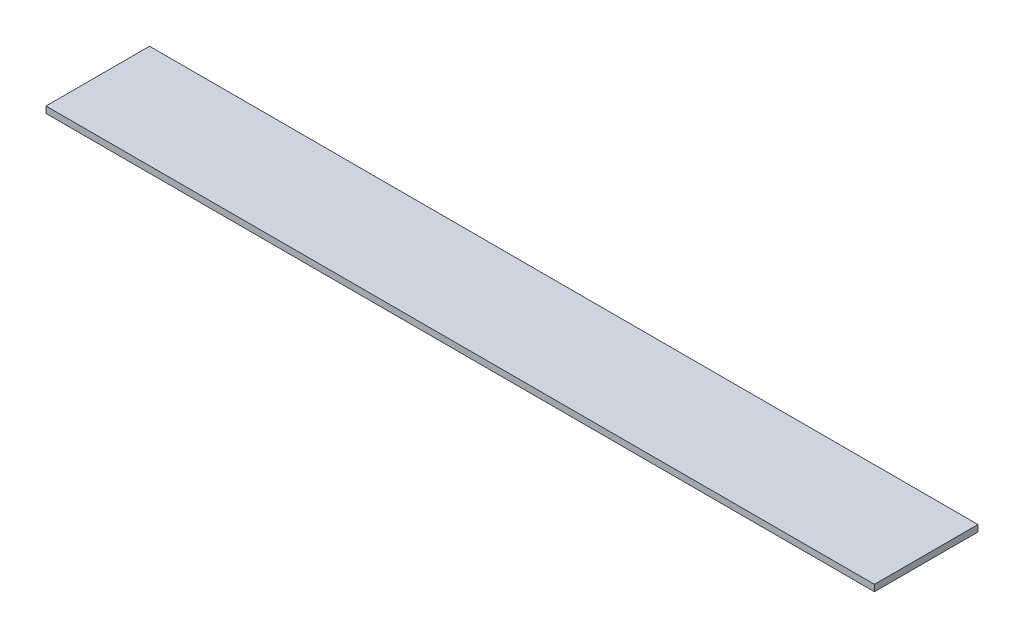
SolidWorks part; units mm, degrees
ref_plane "Front Plane" through (0, 0, 0) normal (0, 0, 1) x (1, 0, 0)
ref_plane "Top Plane" through (0, 0, 0) normal (0, 1, 0) x (1, 0, 0)
ref_plane "Right Plane" through (0, 0, 0) normal (1, 0, 0) x (0, 0, -1)
sketch "Sketch1" plane through (0, 0, 0) normal (0, 1, 0) x (1, 0, 0)
  line L1 (0, 0) -> (203.2, 0)
  line L2 (0, 0) -> (0, 25.4)
  line L3 (0, 25.4) -> (203.2, 25.4)
  line L4 (203.2, 0) -> (203.2, 25.4)
  dimension "D1" = 25.4
  dimension "D2" = 203.2
extrude "Boss-Extrude1" add sketch "Sketch1" along normal blind 1.5875
